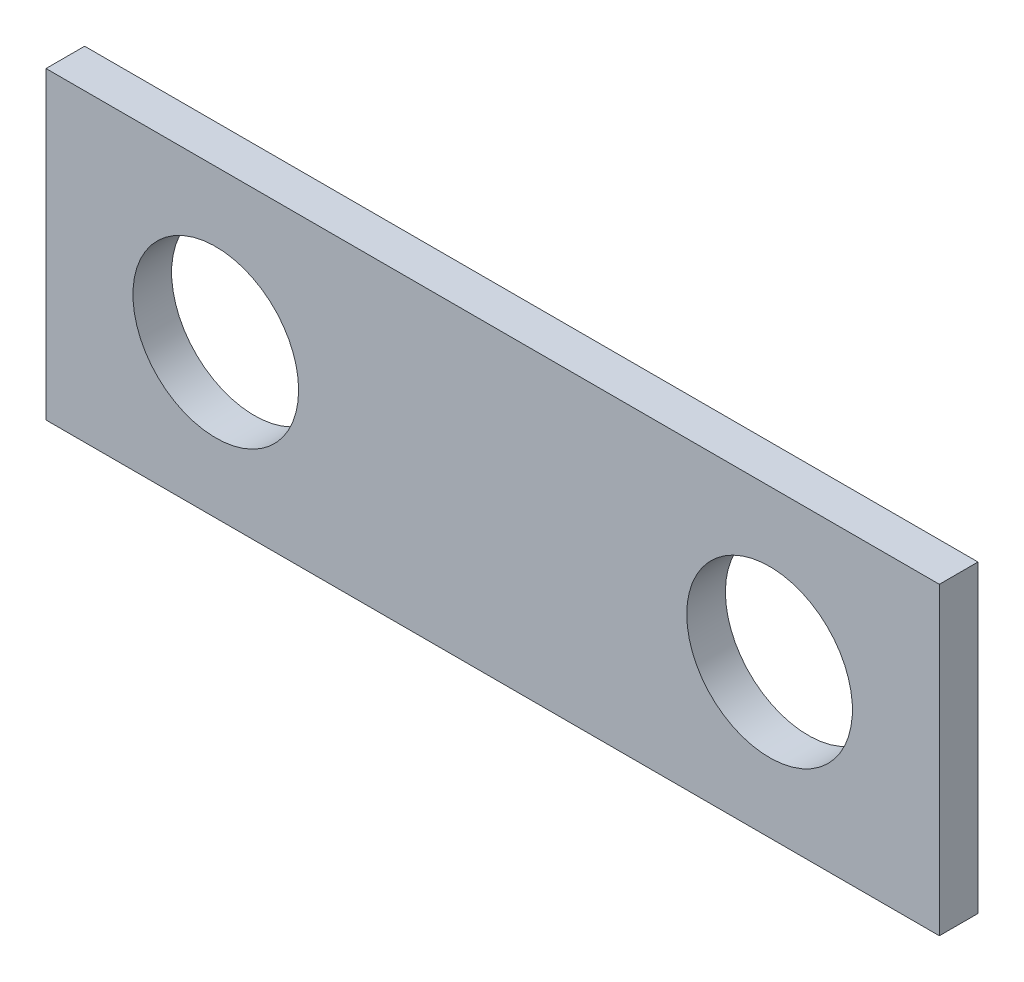
SolidWorks part; units mm, degrees
ref_plane "Front Plane" through (0, 0, 0) normal (0, 0, 1) x (1, 0, 0)
ref_plane "Top Plane" through (0, 0, 0) normal (0, 1, 0) x (1, 0, 0)
ref_plane "Right Plane" through (0, 0, 0) normal (1, 0, 0) x (0, 0, -1)
sketch "Sketch1" plane through (0, 0, 0) normal (0, 0, 1) x (1, 0, 0)
  line L1 (0, 0) -> (19.3802, 0)
  line L2 (0, 0) -> (0, 6.604)
  line L3 (0, 6.604) -> (19.3802, 6.604)
  line L4 (19.3802, 0) -> (19.3802, 6.604)
  dimension "D1" = 19.3802
  dimension "D2" = 6.604
extrude "Boss-Extrude1" add sketch "Sketch1" along normal blind 0.8382
sketch "Sketch2" plane through (0, 0, 0.8382) normal (0, 0, 1) x (1, 0, 0)
  line L0 (0, 3.302) -> (19.3802, 3.302) construction
  line L1 (0, 6.604) -> (0, 0) construction
  line L2 (19.3802, 0) -> (19.3802, 6.604) construction
  line L3 (9.6901, 6.604) -> (9.6901, 0) construction
  line L4 (19.3802, 6.604) -> (0, 6.604) construction
  line L5 (0, 0) -> (19.3802, 0) construction
  line L6 (1.886, 3.302) -> (5.4801, 3.302) construction
  circle A0 centre (3.683, 3.302) radius 1.7971
  circle A1 centre (15.6972, 3.302) radius 1.797
  dimension "D1" = 0
  dimension "D2" = 3.683
extrude "Cut-Extrude1" cut sketch "Sketch2" against normal blind 0.8382
